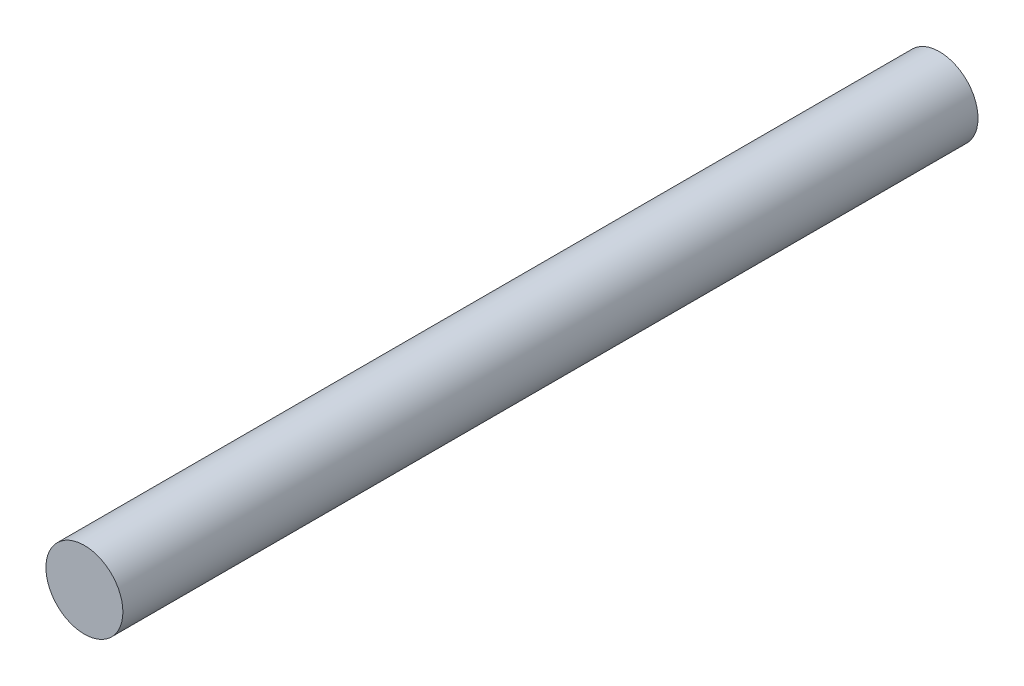
SolidWorks part; units mm, degrees
ref_plane "Piano frontale" through (0, 0, 0) normal (0, 0, 1) x (1, 0, 0)
ref_plane "Piano superiore" through (0, 0, 0) normal (0, 1, 0) x (1, 0, 0)
ref_plane "Piano destro" through (0, 0, 0) normal (1, 0, 0) x (0, 0, -1)
sketch "Schizzo1" plane through (0, 0, 0) normal (0, 0, 1) x (1, 0, 0)
  circle A0 centre (0, 0) radius 1.8
  dimension "D1" = 3.6
extrude "Estrusione-Estrusione1" add sketch "Schizzo1" along normal mid plane 40
